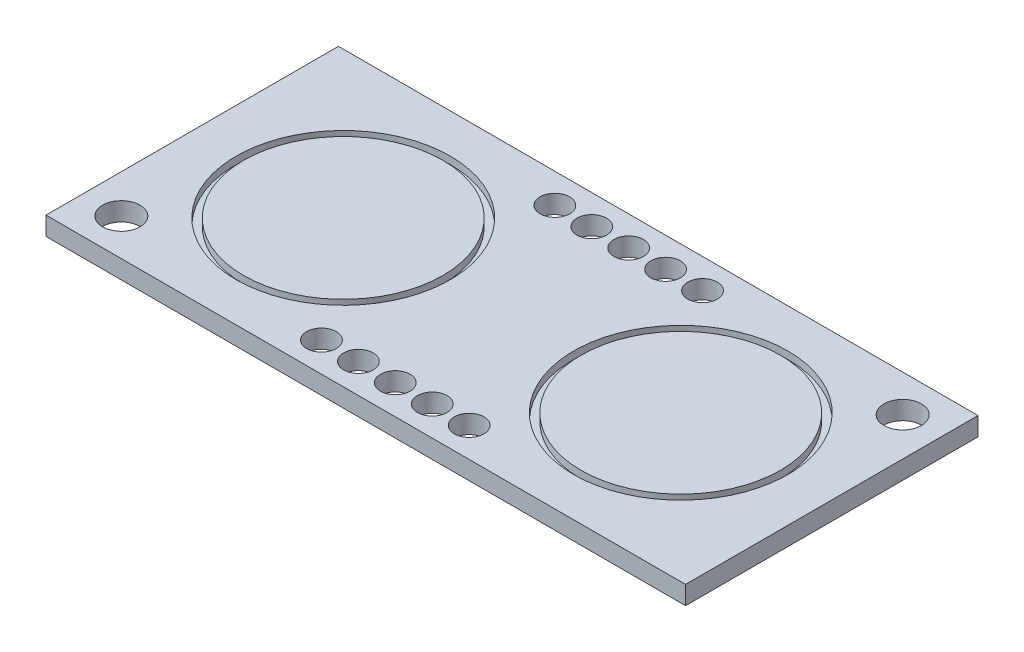
SolidWorks part; units mm, degrees
material "Nylon 6/10"
ref_plane "Front Plane" through (0, 0, 0) normal (0, 0, 1) x (1, 0, 0)
ref_plane "Top Plane" through (0, 0, 0) normal (0, 1, 0) x (1, 0, 0)
ref_plane "Right Plane" through (0, 0, 0) normal (1, 0, 0) x (0, 0, -1)
sketch "Sketch1" plane through (0, 0, 0) normal (0, 1, 0) x (1, 0, 0)
  line L1 (-21.65, 9.9) -> (21.65, 9.9)
  line L2 (-21.65, 9.9) -> (-21.65, -9.9)
  line L3 (-21.65, -9.9) -> (21.65, -9.9)
  line L4 (21.65, 9.9) -> (21.65, -9.9)
  circle A0 centre (-19.05, -7.4) radius 1.27
  circle A1 centre (19.05, 7.4) radius 1.27
  circle A2 centre (0, -7.9) radius 1
  circle A3 centre (0, 7.9) radius 1
  circle A4 centre (2.5, 7.9) radius 1
  circle A5 centre (5, 7.9) radius 1
  circle A6 centre (-2.5, 7.9) radius 1
  circle A7 centre (-5, 7.9) radius 1
  circle A8 centre (-5, -7.9) radius 1
  circle A9 centre (-2.5, -7.9) radius 1
  circle A10 centre (2.5, -7.9) radius 1
  circle A11 centre (5, -7.9) radius 1
  dimension "D9" = 2.54
  dimension "D10" = 2.54
  dimension "D17" = 2
  dimension "D18" = 2
  dimension "D19" = 2
  dimension "D20" = 2
  dimension "D21" = 2
  dimension "D22" = 2
  dimension "D23" = 2
  dimension "D24" = 2
  dimension "D25" = 2
  dimension "D26" = 2
  dimension "D1" = 43.3
  dimension "D2" = 19.8
  dimension "D3" = 21.65
  dimension "D4" = 9.9
  dimension "D5" = 38.1
  dimension "D6" = 14.8
  dimension "D7" = 2.5
  dimension "D8" = 2.6
  dimension "D11" = 2
  dimension "D12" = 2
  dimension "D13" = 2.5
  dimension "D14" = 2.5
  dimension "D15" = 2.5
  dimension "D16" = 2.5
extrude "Extrude1" add sketch "Sketch1" along normal blind 1.25
sketch "Sketch2" plane through (0, 1.25, 0) normal (0, 1, 0) x (1, 0, 0)
  circle A0 centre (-11.425, 0) radius 7.25
  circle A1 centre (-11.425, 0) radius 6.75
  circle A2 centre (11.425, 0) radius 7.25
  circle A3 centre (11.425, 0) radius 6.75
  dimension "D3" = 13.5
  dimension "D4" = 14.5
  dimension "D5" = 13.5
  dimension "D6" = 14.5
  dimension "D1" = 22.85
  dimension "D2" = 11.425
extrude "Extrude2" cut sketch "Sketch2" against normal blind 0.5
